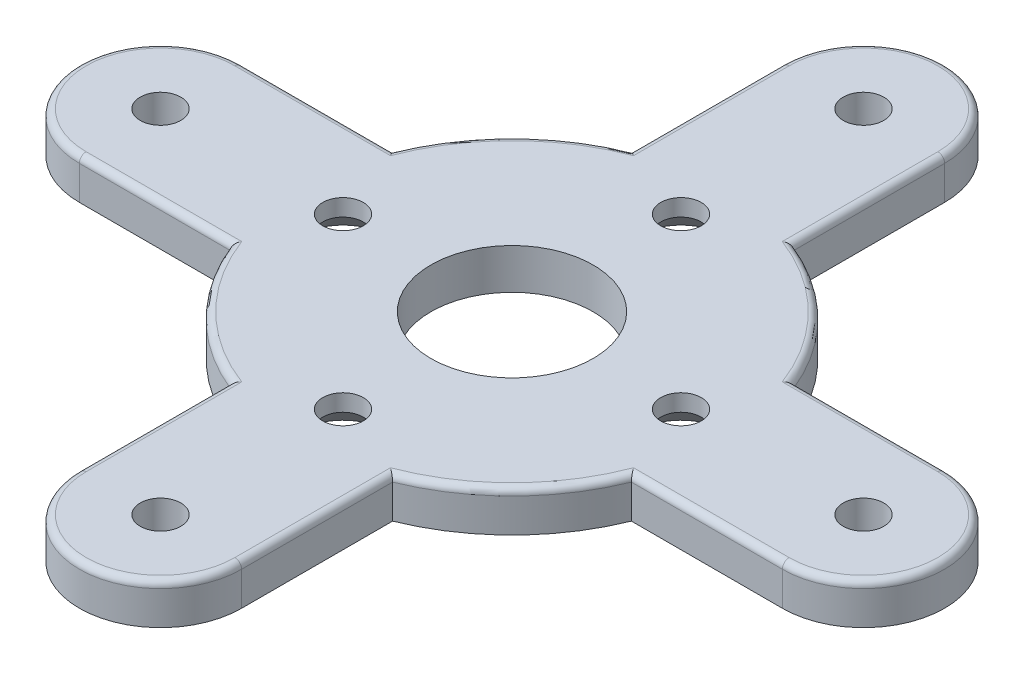
SolidWorks part; units mm, degrees
ref_plane "Ön Düzlem" through (0, 0, 0) normal (0, 0, 1) x (1, 0, 0)
ref_plane "Üst Düzlem" through (0, 0, 0) normal (0, 1, 0) x (1, 0, 0)
ref_plane "Sağ Düzlem" through (0, 0, 0) normal (1, 0, 0) x (0, 0, -1)
sketch "Sketch1" plane through (0, 0, 0) normal (0, 1, 0) x (1, 0, 0)
  line L0 (26, 6) -> (14.8324, 6)
  line L2 (-6, 26) -> (-6, 14.8324)
  line L4 (6, 26) -> (6, 14.8324)
  line L5 (26, -6) -> (14.8324, -6)
  line L6 (6, -26) -> (6, -14.8324)
  line L7 (-6, -26) -> (-6, -14.8324)
  line L8 (-26, -6) -> (-14.8324, -6)
  line L9 (-26, 6) -> (-14.8324, 6)
  arc A0 (-6, 14.8324) -> (-14.8324, 6) centre (0, 0) ccw
  circle A1 centre (0, 0) radius 6
  arc A2 (6, 26) -> (-6, 26) centre (0, 26) ccw
  circle A3 centre (0, 26) radius 1.5
  arc A4 (26, -6) -> (26, 6) centre (26, 0) ccw
  circle A5 centre (26, 0) radius 1.5
  arc A6 (-6, -26) -> (6, -26) centre (0, -26) ccw
  circle A7 centre (0, -26) radius 1.5
  arc A8 (-26, 6) -> (-26, -6) centre (-26, 0) ccw
  circle A9 centre (-26, 0) radius 1.5
  arc A10 (-14.8324, -6) -> (-6, -14.8324) centre (0, 0) ccw
  arc A11 (6, -14.8324) -> (14.8324, -6) centre (0, 0) ccw
  arc A12 (14.8324, 6) -> (6, 14.8324) centre (0, 0) ccw
  point P30 (0, 0)
  dimension "D1" = 16
  dimension "D2" = 12
  dimension "D3" = 3
  dimension "D4" = 12
  dimension "D5" = 26
  dimension "D6" = 4
extrude "Boss-Extrude1" add sketch "Sketch1" along normal blind 3
fillet "Fillet1" radius 0.5 16 edges at (6, 3, -20.4162) (20.4162, 3, -6) (32, 3, 0) (0, 3, 32) (-6, 3, 20.4162) (-11.3137, 3, 11.3137) (-20.4162, 3, 6) (-32, 3, 0) (-20.4162, 3, -6) (-11.3137, 3, -11.3137) (-6, 3, -20.4162) (0, 3, -32) (11.3137, 3, -11.3137) (20.4162, 3, 6) (11.3137, 3, 11.3137) (6, 3, 20.4162)
sketch "Sketch2" plane through (0, 3, 0) normal (0, 1, 0) x (1, 0, 0)
  circle A0 centre (0, 12.5) radius 1.5
  circle A1 centre (12.5, 0) radius 1.5
  circle A2 centre (0, -12.5) radius 1.5
  circle A3 centre (-12.5, 0) radius 1.5
  point P12 (0, 0)
  dimension "D1" = 3
  dimension "D2" = 12.5
  dimension "D3" = 4
extrude "Cut-Extrude1" cut sketch "Sketch2" against normal through all
chamfer "Chamfer1" distance 1.75 angle 45 4 edges at (-12.5, 0, 1.5) (0, 0, -11) (12.5, 0, 1.5) (0, 0, 14)
